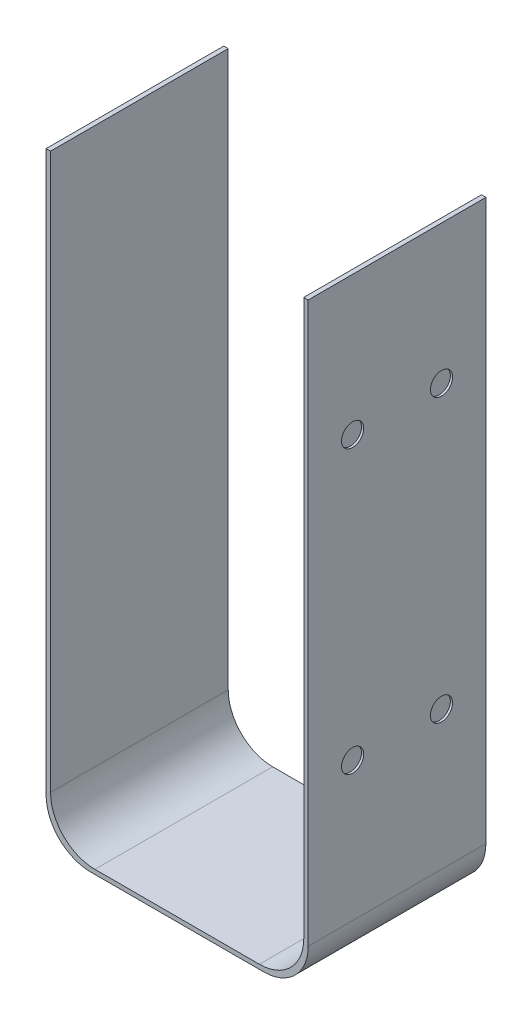
SolidWorks part; units mm, degrees
material "Nikiel"
ref_plane "Płaszczyzna przednia" through (0, 0, 0) normal (0, 0, 1) x (1, 0, 0)
ref_plane "Płaszczyzna górna" through (0, 0, 0) normal (0, 1, 0) x (1, 0, 0)
ref_plane "Płaszczyzna prawa" through (0, 0, 0) normal (1, 0, 0) x (0, 0, -1)
sketch "Szkic1" plane through (0, 0, 0) normal (0, 0, 1) x (1, 0, 0)
  line L0 (-55.6801, 42.8643) -> (-55.6801, 17.8643)
  line L1 (-53.6801, 15.8643) -> (-46.2801, 15.8643)
  line L2 (-44.2801, 17.8643) -> (-44.2801, 42.8643)
  line L3 (-44.2801, 42.8643) -> (-44.0801, 42.8643)
  line L4 (-44.0801, 42.8643) -> (-44.0801, 17.6643)
  line L5 (-46.0801, 15.6643) -> (-53.8801, 15.6643)
  line L6 (-55.8801, 17.6643) -> (-55.8801, 42.8643)
  line L7 (-55.8801, 42.8643) -> (-55.6801, 42.8643)
  arc A0 (-53.6801, 15.8643) -> (-55.6801, 17.8643) centre (-53.6801, 17.8643) cw
  arc A1 (-53.8801, 15.6643) -> (-55.8801, 17.6643) centre (-53.8801, 17.6643) cw
  arc A2 (-44.2801, 17.8643) -> (-46.2801, 15.8643) centre (-46.2801, 17.8643) cw
  arc A3 (-44.0801, 17.6643) -> (-46.0801, 15.6643) centre (-46.0801, 17.6643) cw
  dimension "D1" = 2
  dimension "D2" = 2
  dimension "D3" = 2
  dimension "D4" = 2
extrude "Dodanie-wyciągnięcie1" add sketch "Szkic1" along normal blind 8
sketch "Szkic2" plane through (-44.0801, 0, 0) normal (1, 0, 0) x (0, 0, -1)
  circle A0 centre (-2, 36.6143) radius 0.5
  circle A1 centre (-6, 36.6143) radius 0.5
  circle A2 centre (-6, 23.9143) radius 0.5
  circle A3 centre (-2, 23.9143) radius 0.5
extrude "Wytnij-wyciągnięcie1" cut sketch "Szkic2" against normal blind 0.1
sketch "Szkic3" plane through (-55.8801, 0, 0) normal (-1, 0, 0) x (0, 0, 1)
  circle A0 centre (2, 36.6143) radius 0.5
  circle A1 centre (6, 36.6143) radius 0.5
  circle A2 centre (6, 23.9143) radius 0.5
  circle A3 centre (2, 23.9143) radius 0.5
extrude "Wytnij-wyciągnięcie2" cut sketch "Szkic3" against normal blind 0.1
